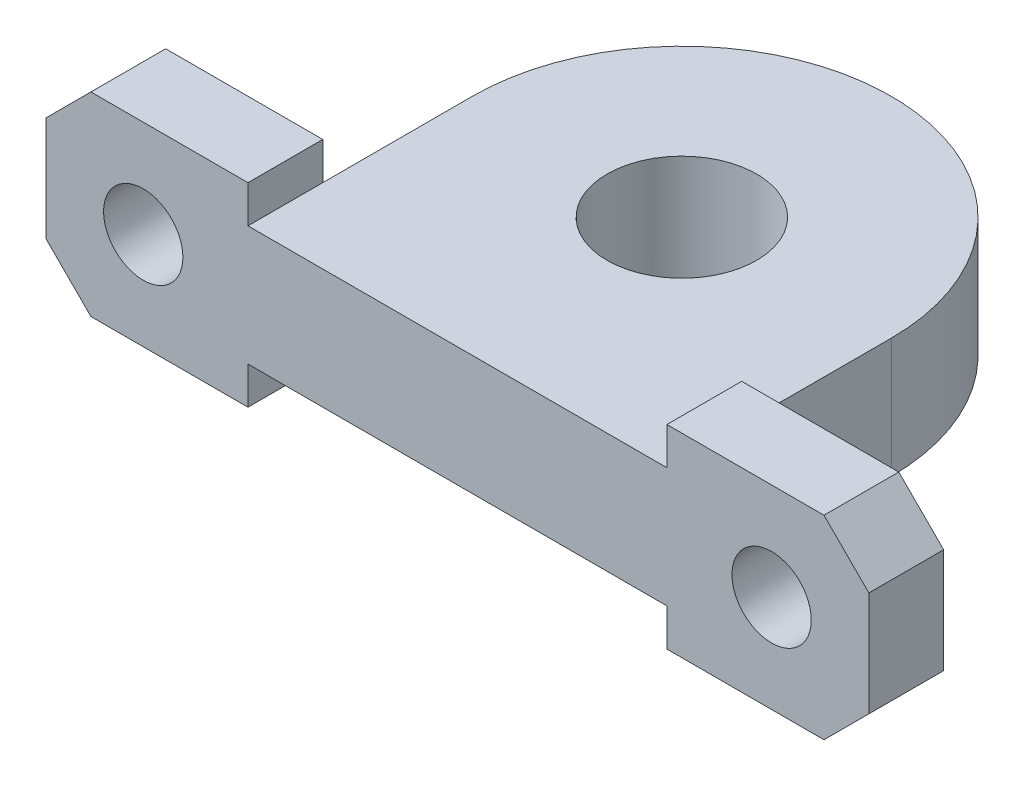
SolidWorks part; units mm, degrees
material "1100-H16 Rod (SS)"
ref_plane "前视基准面" through (0, 0, 0) normal (0, 0, 1) x (1, 0, 0)
ref_plane "上视基准面" through (0, 0, 0) normal (0, 1, 0) x (1, 0, 0)
ref_plane "右视基准面" through (0, 0, 0) normal (1, 0, 0) x (0, 0, -1)
other "Configuration Table"
sketch "Sketch1" plane through (0, 0, 0) normal (0, 0, 1) x (1, 0, 0)
  line L0 (15, 0) -> (15, 8)
  line L1 (15, 0) -> (-15, 0)
  line L2 (0, 0) -> (0, 8)
  line L3 (15, 8) -> (-15, 8)
  line L4 (-15, 0) -> (-15, 8)
  line L5 (-27.5, 10.5) -> (-14, 10.5)
  line L6 (-27.5, 10.5) -> (-27.5, -2.5)
  line L7 (-27.5, -2.5) -> (-14, -2.5)
  line L8 (-14, 10.5) -> (-14, -2.5)
  line L9 (27.5, -2.5) -> (14, -2.5)
  line L10 (14, 10.5) -> (14, -2.5)
  line L11 (27.5, 10.5) -> (14, 10.5)
  line L12 (27.5, 10.5) -> (27.5, -2.5)
  circle A0 centre (-21, 4) radius 2.65
  circle A1 centre (21, 4) radius 2.65
  point P19 (-14, 4)
  point P20 (0, 4)
  dimension "D8" = 5.3
  dimension "D1" = 13
  dimension "D2" = 42
  dimension "D3" = 30
  dimension "D4" = 28
  dimension "D5" = 55
  dimension "D6" = 13.5
  dimension "D7" = 8
extrude "Boss-Extrude1" add sketch "Sketch1" along normal blind 5 contours L8 L5 L6 L7 L1 L4 L3 A0 | L8 L3 L4 L1 | L3 L8 L1 L2 | L10 L3 L2 L1 | L3 L10 L1 L0 | L12 L11 L10 L3 L0 L1 L9 A1
chamfer "Chamfer1" distance 3 angle 45 4 edges at (27.5, 10.5, 2.5) (27.5, -2.5, 2.5) (-27.5, -2.5, 2.5) (-27.5, 10.5, 2.5)
ref_plane "Plane1" through (0, 4, 0) normal (0, 1, 0) x (1, 0, 0)
sketch "Sketch2" plane through (0, 4, 0) normal (0, 1, 0) x (1, 0, 0)
  line L0 (-14, -5) -> (-14, 10)
  line L1 (0, -5) -> (0, 9.4963) construction
  line L3 (14, -5) -> (14, 10)
  line L4 (-14, -5) -> (14, -5)
  arc A0 (-14, 10) -> (14, 10) centre (0, 10) cw
  dimension "D1" = 15
extrude "Boss-Extrude2" add sketch "Sketch2" along normal mid plane 8
sketch "Sketch3" plane through (0, 8, 0) normal (0, 1, 0) x (1, 0, 0)
  circle A0 centre (0, 10) radius 5
  dimension "D1" = 10
extrude "Cut-Extrude1" cut sketch "Sketch3" against normal through all
